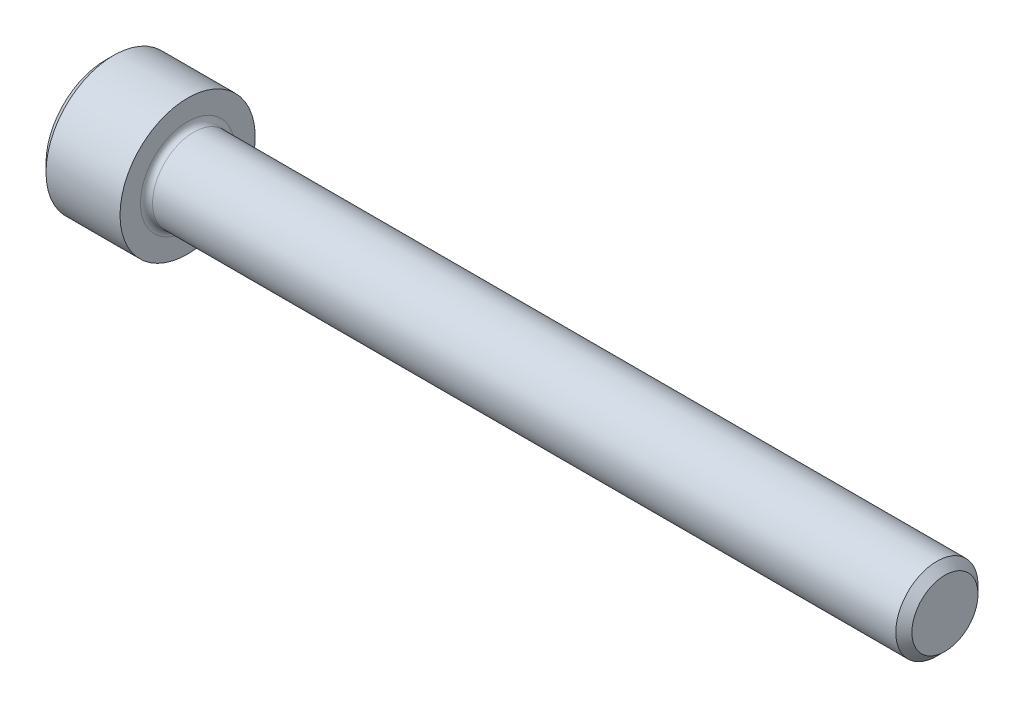
SolidWorks part; units mm, degrees
ref_plane "Plane1" through (0, 0, 0) normal (0, 0, 1) x (1, 0, 0)
ref_plane "Plane2" through (0, 0, 0) normal (0, 1, 0) x (1, 0, 0)
ref_plane "Plane3" through (0, 0, 0) normal (1, 0, 0) x (0, 0, -1)
sketch "BodySke" plane through (0, 0, 0) normal (0, 0, 1) x (1, 0, 0)
  line L0 (0, 0) -> (0, 3.4862)
  line L1 (0.4826, 3.9687) -> (4.826, 3.9687)
  line L2 (4.826, 3.9687) -> (4.826, 2.413)
  line L3 (4.826, 2.413) -> (48.8036, 2.413)
  line L4 (49.276, 1.9406) -> (49.276, 0)
  line L5 (49.276, 0) -> (0, 0)
  line L6 (-31.75, 0) -> (127, 0) construction
  line L7 (0, 3.4862) -> (0.4826, 3.9687)
  line L8 (49.276, 1.9406) -> (48.8036, 2.413)
  line L9 (0, -3.4862) -> (0.4826, -3.9688) construction
  line L10 (49.276, -1.9406) -> (48.8036, -2.413) construction
  line L11 (5.6185, 9.525) -> (5.6185, 3.175) construction
  line L12 (4.826, 9.525) -> (4.826, 3.175) construction
  line L13 (11.176, 9.525) -> (11.176, 3.175) construction
  dimension "Diameter" = 4.826
  dimension "Head_ht" = 4.826
  dimension "Length" = 44.45
  dimension "Body_ch_ang" = 45
  dimension "Head_dia" = 7.9375
  dimension "Head_ch_ang" = 45
  dimension "Head_side_ht" = 4.3434
  dimension "Minor_dia" = 3.8811
  dimension "Advance" = 0.7925
  dimension "Thread_nom" = 44.45
  dimension "Thread_length" = 38.1
revolve "Base-Revolve" add sketch "BodySke"
cosmetic thread "ThreadCosmetic"
fillet "Fillet1" radius 0.3556
sketch "Sketch2" plane through (0, 0, 0) normal (0, 0, 1) x (1, 0, 0)
  line L0 (0, 1.985) -> (2.286, 1.985)
  line L1 (2.286, 1.985) -> (3.432, 0)
  line L2 (-31.75, 0) -> (127, 0) construction
  line L3 (3.432, 0) -> (0, 0)
  line L4 (0, 0) -> (0, 1.985)
  line L5 (0, 3.4862) -> (0, -3.4862) construction
  line L6 (0, 0) -> (47.625, 0) construction
  line L7 (4.826, -3.9687) -> (4.826, 3.9687) construction
  dimension "D1" = 1.985
  dimension "D2" = 60
  dimension "Wall_thickness" = 2.54
revolve "Hex-PreBroach" cut sketch "Sketch2" angle 360 about L6
sketch "Sketch3" plane through (0, 0, 0) normal (-1, 0, 0) x (0, 0.5, 0.866)
  line L0 (1.146, 1.985) -> (-1.146, 1.985)
  line L1 (-1.146, 1.985) -> (-2.2921, 0)
  line L2 (1.146, 1.985) -> (2.2921, 0)
  line L3 (1.146, -1.985) -> (2.2921, 0)
  line L4 (1.146, -1.985) -> (-1.146, -1.985)
  line L5 (-1.146, -1.985) -> (-2.2921, 0)
  dimension "D1" = 1.985
  dimension "D2" = 1.985
  dimension "Hex_size" = 3.97
extrude "Hex" cut sketch "Sketch3" against normal blind 2.286
sketch "Sketch4" plane through (0, 0, 0) normal (-1, 0, 0) x (0, 0, 1)
  line L0 (0, 0) -> (2.3876, 0)
  line L1 (0, 0) -> (6.1484, 3.5498) construction
  line L2 (0, 0) -> (1.1938, 2.0677)
  line L3 (1.9883, 0.576) -> (2.2704, 0.7389)
  line L4 (1.493, 1.4339) -> (1.7751, 1.5968)
  arc A0 (1.9883, 0.576) -> (1.493, 1.4339) centre (0, 0) ccw
  arc A1 (2.3876, 0) -> (2.2704, 0.7389) centre (0, 0) ccw
  arc A2 (1.1938, 2.0677) -> (1.7751, 1.5968) centre (0, 0) cw
  dimension "D1" = 30
  dimension "Spline_n_dim" = 4.1402
  dimension "Spline_m_dim" = 4.7752
  dimension "D2" = 60
  dimension "D3" = 0.4953
  dimension "Spline_p_dim" = 0.9906
extrude "Spline" [suppressed] cut sketch "Sketch4" against normal blind 2.286
pattern_circular "CirPattern1" [suppressed] count 6 every 60
sketch "Sketch5" plane through (0, 0, 0) normal (0, 0, 1) x (1, 0, 0)
  line L0 (-31.75, 0) -> (127, 0) construction
  line L2 (0, 3.4862) -> (0, -3.4862) construction
  circle A0 centre (1.651, 0) radius 0.5905
  dimension "Drilled_hole_dia" = 1.1811
  dimension "Drilled_hole_loc" = 1.651
extrude "Hole" [suppressed] cut sketch "Sketch5" against normal through all and the other way through all
pattern_circular "Drilled-4" [suppressed] count 2 every 60
pattern_circular "Drilled-6" [suppressed] count 3 every 60
sketch "ThdSchSke" plane through (0, 0, 0) normal (0, 0, 1) x (1, 0, 0)
  line L0 (5.6185, -1.9406) -> (5.2877, -2.413)
  line L1 (5.6185, -1.9406) -> (5.9493, -2.413)
  line L2 (5.9493, -2.413) -> (5.9493, -3.0163)
  line L3 (-3.175, 0) -> (5.1513, 0) construction
  line L5 (5.9493, -3.0163) -> (5.2877, -3.0163)
  line L6 (5.2877, -3.0163) -> (5.2877, -2.413)
  line L7 (0, 3.4862) -> (0, -3.4862) construction
  dimension "Thread_minor" = 3.8811
  dimension "Diameter" = 4.826
  dimension "Start" = 5.6185
  dimension "SideAngle" = 55
  dimension "VeeAngle" = 70
  dimension "Overcut" = 6.0325
revolve "ThreadSchematic" [suppressed] cut sketch "ThdSchSke" angle 360 about L3
pattern_linear "ThdSchPat" [suppressed]
equation "\"D2@Sketch3\" = \"Hex_size@Sketch3\" / 2"
equation "\"D1@Sketch3\" = \"Hex_size@Sketch3\" / 2"
equation "\"D1@Sketch2\" = \"Hex_size@Sketch3\" / 2"
equation "\"D3@Sketch4\" = \"Spline_p_dim@Sketch4\" / 2"
equation "\"Thread_minor@ThreadCosmetic\"  =  \"Minor_dia@BodySke\""
equation "\"D2@CirPattern1\" = 360 / \"Num_teeth@CirPattern1\""
equation "\"Wall_thickness@Sketch2\" = \"Head_ht@BodySke\" - \"Key_eng@Hex\""
equation "\"Thread_length@ThreadCosmetic\" = ((sgn( (\"Length@BodySke\" - \"Advance@BodySke\" ) - \"Thread_nom@BodySke\" )-1)*( (\"Length@BodySke\" - \"Advance@BodySke\" ) - \"Thread_nom@BodySke\" ))/-2+ \"Thread_nom@BodySke\""
equation "\"Thread_minor@ThdSchSke\" = \"Minor_dia@BodySke\""
equation "\"Diameter@ThdSchSke\" = \"Diameter@BodySke\""
equation "\"Overcut@ThdSchSke\" = \"Diameter@BodySke\" * 1.25"
equation "\"Start@ThdSchSke\" = \"Head_ht@BodySke\" + \"Length@BodySke\" - \"Thread_length@ThreadCosmetic\"  '---Non-countersunk---"
equation "\"Num_threads@ThdSchPat\" = int( \"Thread_length@ThreadCosmetic\" / \"Advance@BodySke\" + 0.999 )  + 1"
equation "\"Advance@ThdSchPat\" = \"Thread_length@ThreadCosmetic\" /  (\"Num_threads@ThdSchPat\" - 1) 'relax it"
equation "\"Num_threads@ThdSchPat\" = \"Num_threads@ThdSchPat\" - sgn( \"Num_threads@ThdSchPat\" - 1) '---chamfered tips only---"
